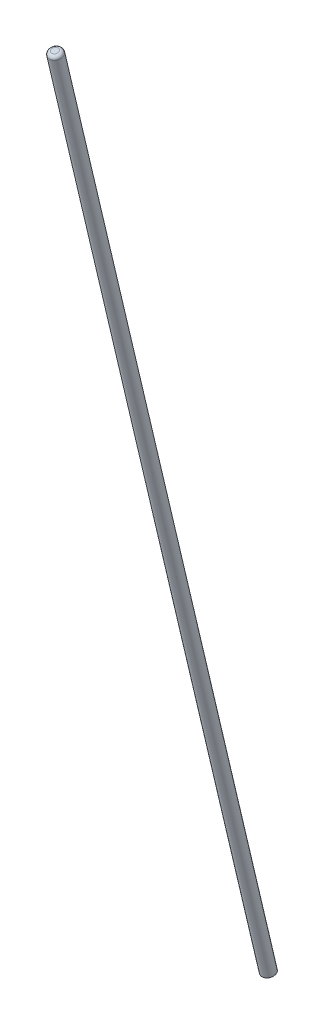
SolidWorks part; units mm, degrees
ref_plane "Front Plane" through (0, 0, 0) normal (0, 0, 1) x (1, 0, 0)
ref_plane "Top Plane" through (0, 0, 0) normal (0, 1, 0) x (1, 0, 0)
ref_plane "Right Plane" through (0, 0, 0) normal (1, 0, 0) x (0, 0, -1)
sketch3d "3DSketch1"
  line L0 (1209.7508, 1821.5171, 1121.2546) -> (1209.7508, 1816.4908, 1121.2546) construction
  line L1 (1209.7508, 1821.5171, 1121.2546) -> (1209.7508, 1770.7171, 1121.2546) construction
  line L2 (1209.7508, 1816.4908, 1121.2546) -> (1204.7245, 1816.4908, 1121.2546) construction
  line L3 (1204.7245, 1816.4908, 1121.2546) -> (1204.6708, 1816.5445, 948.5346) construction
  line L4 (1204.6708, 1816.4371, 948.5346) -> (1031.9508, 1816.4371, 948.5346) construction
  line L7 (1209.7508, 2531.8162, 1121.2546) -> (1037.0308, 2531.8162, 1121.2546) construction
  line L8 (1209.7508, 2608.9171, 1121.2546) -> (1209.7508, 1821.5171, 1121.2546) construction
  line L9 (1158.9508, 2608.9171, 1121.2546) -> (-86.1675, 1821.5171, 1121.2546) construction
  line L11 (1031.9508, 1816.4371, 948.5346) -> (1037.0308, 2531.8162, 1121.2546)
  circle A0 centre (1204.7245, 1816.4908, 1121.2546) radius 5.0263 construction
  circle A1 centre (1204.6708, 1816.4371, 948.5346) radius 5.08 construction
  point P5 (1204.7245, 1816.4908, 1126.2809)
  point P14 (1209.7508, 1816.4371, 948.5346)
  dimension "D1" = 172.72
  dimension "D2" = 172.72
  dimension "D4" = 172.72
sweep "Sweep1" add path "3DSketch1" circular profile diameter 10.16 parameters "D3"=10.16
fillet "Fillet1" radius 2.54 1 edges at (1037.0308, 2530.6239, 1126.1927)
